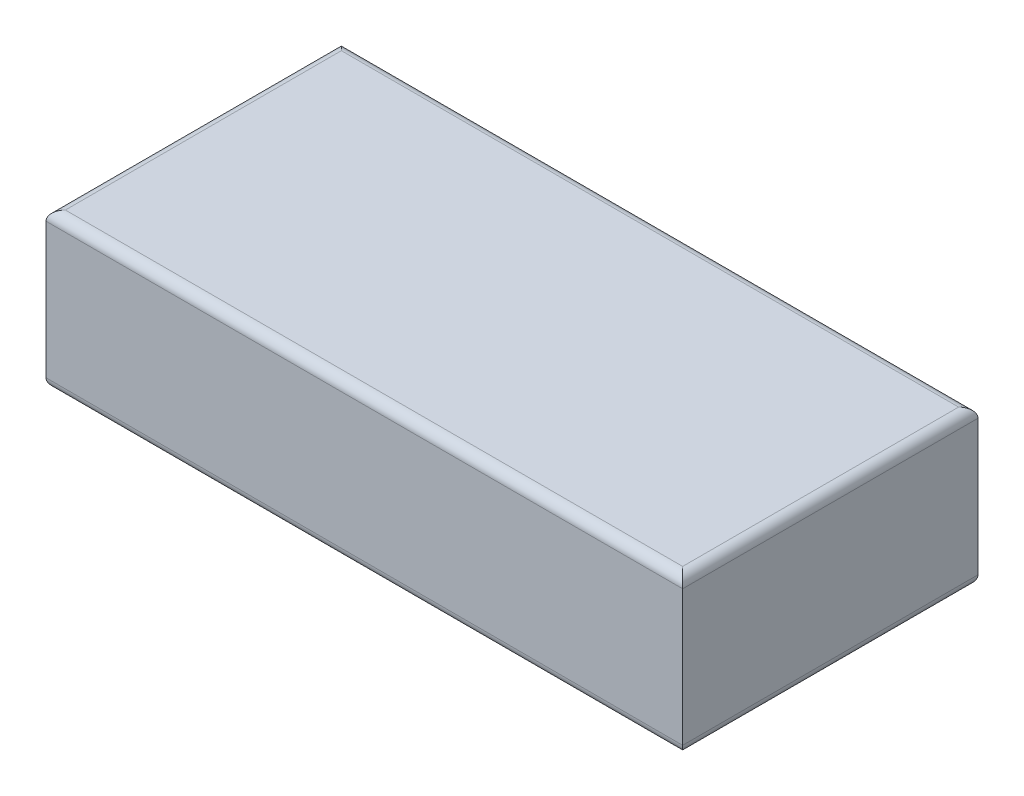
SolidWorks part; units mm, degrees
ref_plane "Front Plane" through (0, 0, 0) normal (0, 0, 1) x (1, 0, 0)
ref_plane "Top Plane" through (0, 0, 0) normal (0, 1, 0) x (1, 0, 0)
ref_plane "Right Plane" through (0, 0, 0) normal (1, 0, 0) x (0, 0, -1)
sketch "Sketch1" plane through (0, 0, 0) normal (0, 1, 0) x (1, 0, 0)
  line L1 (0, 0) -> (263, 0)
  line L2 (0, 0) -> (0, 122)
  line L3 (0, 122) -> (263, 122)
  line L4 (263, 0) -> (263, 122)
extrude "Boss-Extrude1" add sketch "Sketch1" along normal blind 64
fillet "Fillet1" radius 4 8 edges at (263, 0, -61) (131.5, 0, -122) (0, 0, -61) (131.5, 0, 0) (263, 64, -61) (131.5, 64, -122) (0, 64, -61) (131.5, 64, 0)
sketch "Sketch2" plane through (0, 64, 0) normal (0, 1, 0) x (1, 0, 0)
  text T0 "BATTERY" font "Century Gothic" height 40
